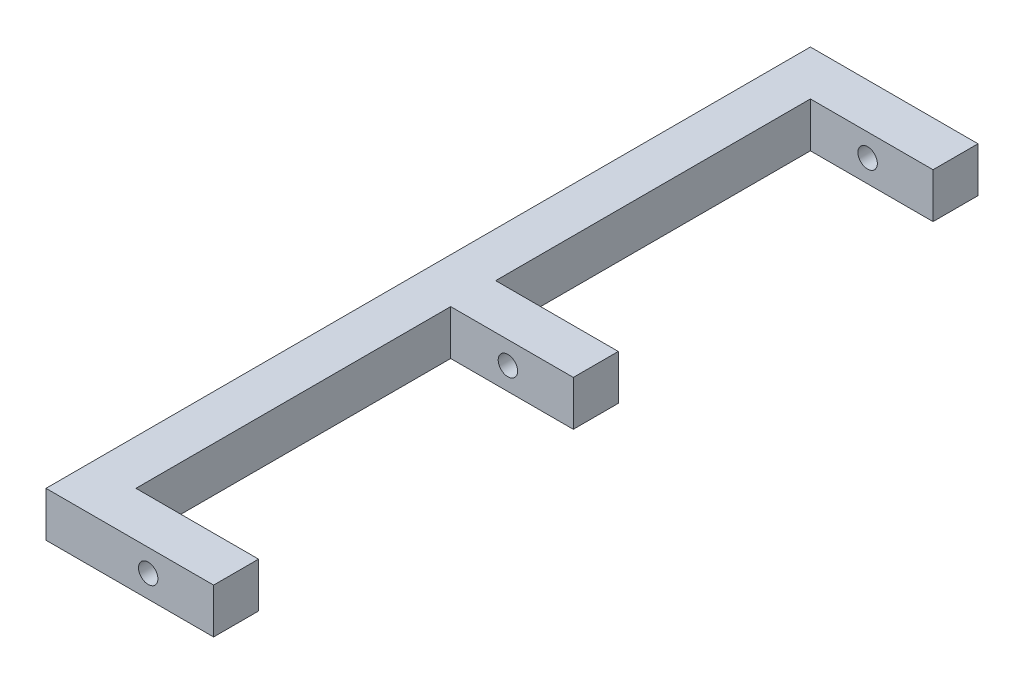
SolidWorks part; units mm, degrees
ref_plane "Plan de face" through (0, 0, 0) normal (0, 0, 1) x (1, 0, 0)
ref_plane "Plan de dessus" through (0, 0, 0) normal (0, 1, 0) x (1, 0, 0)
ref_plane "Plan de droite" through (0, 0, 0) normal (1, 0, 0) x (0, 0, -1)
sketch "Esquisse1" plane through (0, 0, 0) normal (0, 0, 1) x (1, 0, 0)
  line L1 (0, 0) -> (22, 0)
  line L2 (0, 0) -> (0, 22)
  line L3 (0, 22) -> (22, 22)
  line L4 (22, 0) -> (22, 22)
  dimension "D1" = 22
  dimension "D2" = 22
extrude "Extrusion1" add sketch "Esquisse1" along normal blind 374
sketch "Esquisse2" plane through (22, 0, 0) normal (1, 0, 0) x (0, 0, -1)
  line L0 (-374, 11) -> (0, 11) construction
  line L1 (-374, 0) -> (-374, 22) construction
  line L2 (0, 0) -> (0, 22) construction
  line L3 (-187, 0) -> (-187, 22) construction
  line L4 (-374, 0) -> (0, 0) construction
  line L5 (-374, 22) -> (0, 22) construction
  line L6 (-22, 22) -> (-22, 0)
  line L7 (-374, 22) -> (-352, 22)
  line L8 (-374, 22) -> (-374, 0)
  line L9 (-374, 0) -> (-352, 0)
  line L10 (-352, 22) -> (-352, 0)
  line L11 (-198, 22) -> (-176, 22)
  line L12 (-198, 22) -> (-198, 0)
  line L13 (-198, 0) -> (-176, 0)
  line L14 (-176, 22) -> (-176, 0)
  line L15 (0, 0) -> (-22, 0)
  line L16 (0, 22) -> (0, 0)
  line L17 (0, 22) -> (-22, 22)
  dimension "D1" = 22
  dimension "D2" = 22
extrude "Extrusion2" add sketch "Esquisse2" along normal blind 60
sketch "Esquisse3" plane through (0, 0, 374) normal (0, 0, 1) x (1, 0, 0)
  line L0 (82, 11) -> (0, 11) construction
  line L1 (82, 22) -> (82, 0) construction
  line L2 (0, 22) -> (0, 0) construction
  line L3 (50, 22) -> (50, 0) construction
  line L4 (82, 22) -> (0, 22) construction
  line L5 (0, 0) -> (82, 0) construction
  circle A0 centre (50, 11) radius 4.75
  dimension "D2" = 9.5
  dimension "D1" = 50
extrude "Extrusion3" cut sketch "Esquisse3" against normal up to surface (374 mm away) up to face at (41, 11, 0)
